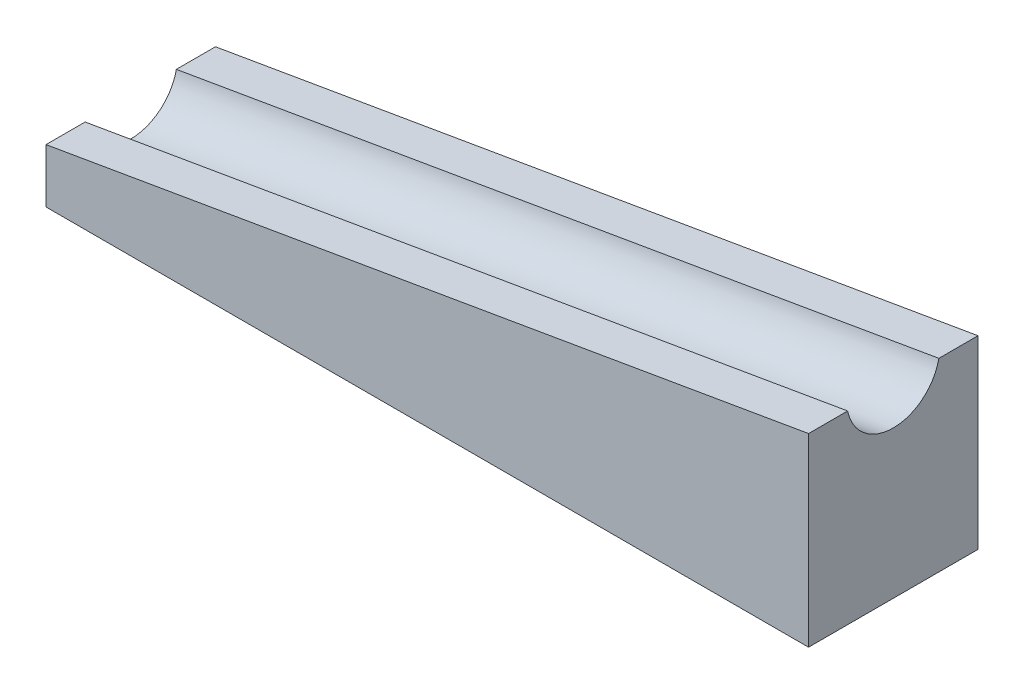
SolidWorks part; units mm, degrees
ref_plane "Front Plane" through (0, 0, 0) normal (0, 0, 1) x (1, 0, 0)
ref_plane "Top Plane" through (0, 0, 0) normal (0, 1, 0) x (1, 0, 0)
ref_plane "Right Plane" through (0, 0, 0) normal (1, 0, 0) x (0, 0, -1)
sketch "Sketch2" plane through (0, 0, 0) normal (0, 0, 1) x (1, 0, 0)
  line L0 (0, 0) -> (90, 0) construction
  line L1 (90, 0) -> (90, 15.4648)
  line L2 (90, 15.4648) -> (0, 0)
  line L3 (0, -6.3784) -> (0, 0)
  line L4 (0, -6.3784) -> (90, -6.3784)
  line L5 (90, -6.3784) -> (90, 0)
  dimension "D1" = 9.75
  dimension "D2" = 90
extrude "Boss-Extrude1" add sketch "Sketch2" along normal blind 20
sketch "Sketch3" plane through (90, 0, 0) normal (1, 0, 0) x (0, 0, -1)
  line L0 (-20, 15.4648) -> (0, 15.4648) construction
  line L1 (0, 15.4648) -> (-10, 15.4648) construction
  line L2 (-20, 15.4648) -> (0, 15.4648) construction
  line L3 (-10, 15.4648) -> (-10, 8.8049) construction
  line L4 (-11.9799, 15.4648) -> (-8.0201, 15.4648)
  arc A0 (-11.9799, 15.4648) -> (-8.0201, 15.4648) centre (-10, 8.8049) ccw
  arc A1 (-8.0201, 15.4648) -> (-11.9799, 15.4648) centre (-10, 8.8049) ccw construction
  point P4 (0, 0)
ref_plane "Plane1" through (90, 15.4648, 0) normal (0.9856, 0.1693, 0) x (0, 0, -1)
ref_plane "Plane2" through (90, 15.4648, 0) normal (0.9856, 0.1693, 0) x (0, 0, -1)
sketch "Sketch5" plane through (90, 15.4648, 0) normal (0.9856, 0.1693, 0) x (0, 0, -1)
  line L0 (-20, 0) -> (0, 0) construction
  line L1 (-10, 0) -> (-10, 1.1334) construction
  line L2 (-15.3819, 0) -> (-4.6181, 0)
  arc A0 (-15.3819, 0) -> (-4.6181, 0) centre (-10, 1.1334) ccw
  arc A1 (-4.6181, 0) -> (-15.3819, 0) centre (-10, 1.1334) ccw construction
  point P8 (0, 0)
  dimension "D1" = 5.5
extrude "Cut-Extrude1" cut sketch "Sketch5" against normal through all
